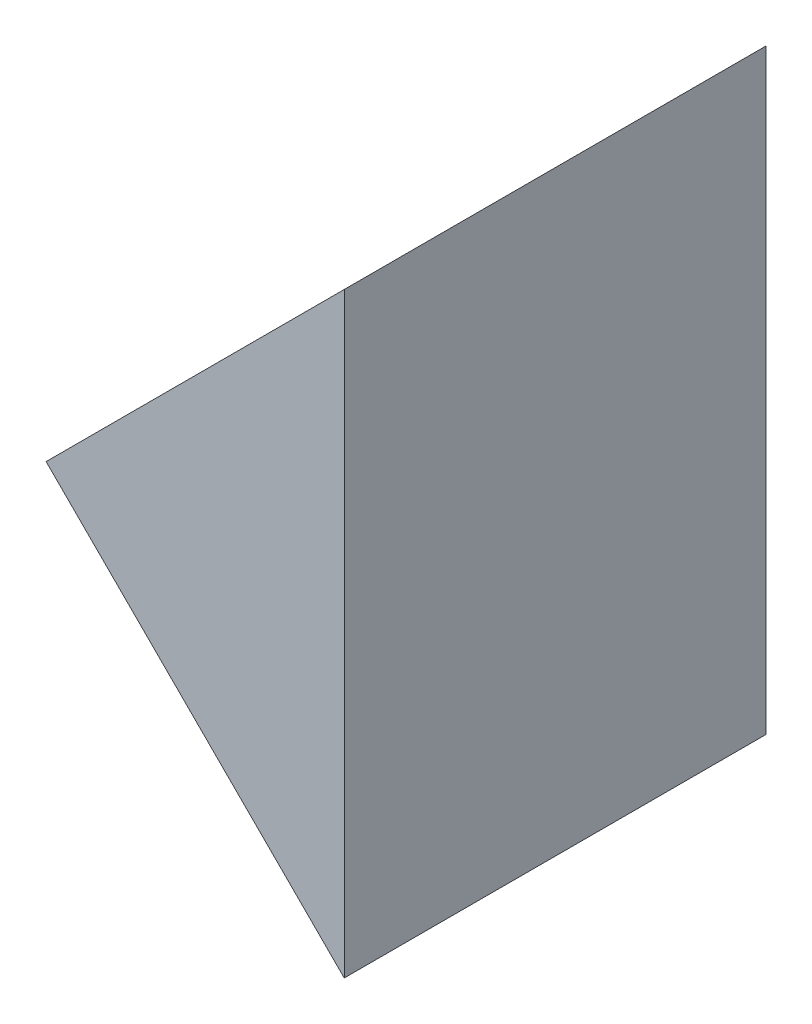
SolidWorks part; units mm, degrees
ref_plane "前视基准面" through (0, 0, 0) normal (0, 0, 1) x (1, 0, 0)
ref_plane "上视基准面" through (0, 0, 0) normal (0, 1, 0) x (1, 0, 0)
ref_plane "右视基准面" through (0, 0, 0) normal (1, 0, 0) x (0, 0, -1)
sketch "草图1" plane through (0, 0, 0) normal (0, 0, 1) x (1, 0, 0)
  line L0 (55.4767, 13.7757) -> (59.0122, 17.3112)
  line L1 (55.4767, 13.7757) -> (59.0122, 10.2402)
  line L2 (59.0122, 10.2402) -> (59.0122, 17.3112)
  dimension "D1" = 5
  dimension "D2" = 5
extrude "凸台-拉伸1" add sketch "草图1" along normal blind 5
